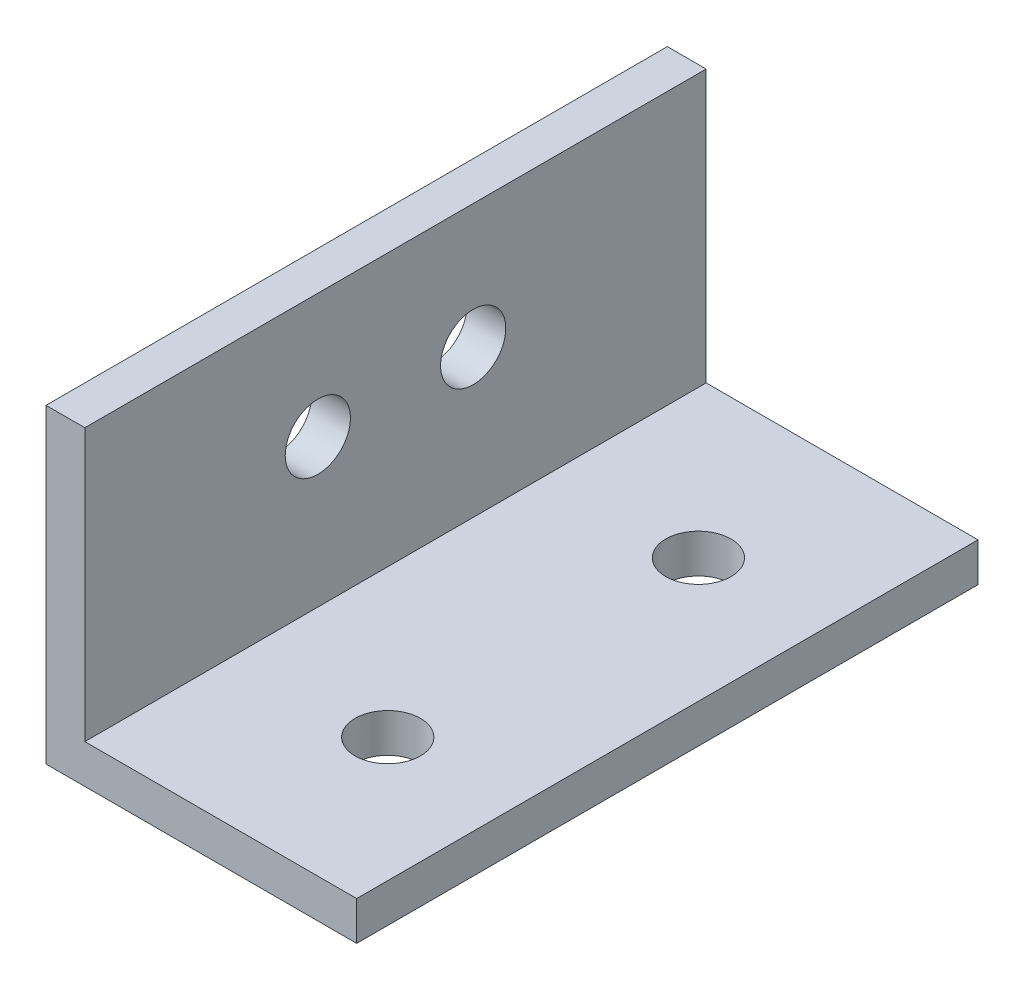
SolidWorks part; units mm, degrees
ref_plane "Front Plane" through (0, 0, 0) normal (0, 0, 1) x (1, 0, 0)
ref_plane "Top Plane" through (0, 0, 0) normal (0, 1, 0) x (1, 0, 0)
ref_plane "Right Plane" through (0, 0, 0) normal (1, 0, 0) x (0, 0, -1)
sketch "Sketch2" plane through (0, 0, 0) normal (0, 0, 1) x (1, 0, 0)
  line L1 (0, 0) -> (3.175, 0)
  line L2 (0, 0) -> (0, 25.4)
  line L3 (0, 25.4) -> (3.175, 25.4)
  line L4 (3.175, 0) -> (3.175, 25.4)
  line L5 (0, 0) -> (25.4, 0)
  line L6 (0, 0) -> (0, 3.175)
  line L7 (0, 3.175) -> (25.4, 3.175)
  line L8 (25.4, 0) -> (25.4, 3.175)
  dimension "D1" = 25.4
  dimension "D2" = 25.4
  dimension "D3" = 3.175
  dimension "D4" = 3.175
extrude "Boss-Extrude1" add sketch "Sketch2" along normal blind 50.8 contours L5 L8 L7 L4 | L7 L2 L1 L4 | L2 L7 L4 L3
sketch "Sketch3" plane through (0, 0, 0) normal (-1, 0, 0) x (0, 0, 1)
  line L1 (0, 3.175) -> (0, 25.4) construction
  line L2 (50.8, 0) -> (0, 0) construction
  circle A2 centre (19.05, 15.24) radius 2.667
  circle A3 centre (31.75, 15.24) radius 2.667
  dimension "D2" = 15.24
  dimension "D3" = 19.05
  dimension "D5" = 5.334
  dimension "D6" = 5.334
  dimension "D1" = 12.7
extrude "Cut-Extrude1" cut sketch "Sketch3" against normal up to surface (3.175 mm away) contours A3 | A2 up to face at (3.175, 14.2875, 25.4)
sketch "Sketch4" plane through (0, 0, 0) normal (0, -1, 0) x (1, 0, 0)
  line L2 (0, 50.8) -> (0, 0) construction
  line L4 (0, 0) -> (25.4, 0) construction
  line L5 (0, 50.8) -> (25.4, 50.8) construction
  circle A0 centre (15.24, 38.1) radius 2.667
  circle A1 centre (15.24, 12.7) radius 2.667
  dimension "D2" = 12.7
  dimension "D3" = 15.24
  dimension "D4" = 12.7
  dimension "D1" = 15.24
extrude "Cut-Extrude2" cut sketch "Sketch4" against normal up to surface (3.175 mm away) contours A0 | A1 up to face at (14.2875, 3.175, 25.4)
